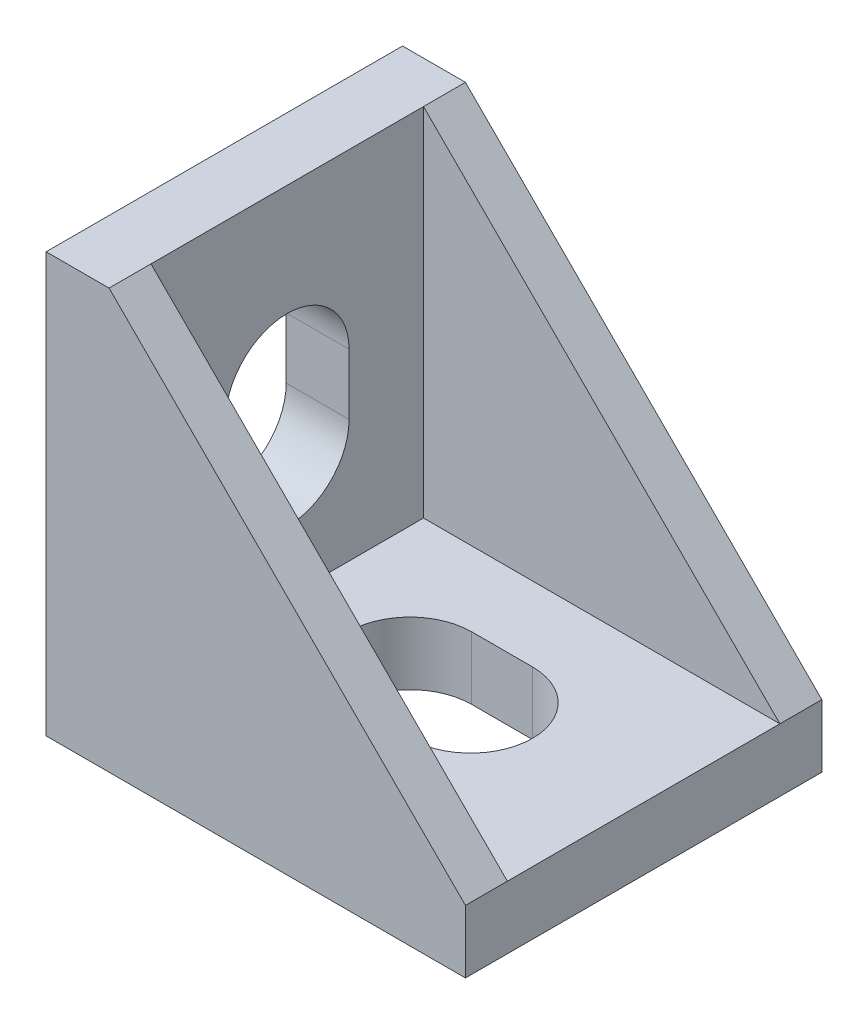
SolidWorks part; units mm, degrees
ref_plane "前视基准面" through (0, 0, 0) normal (0, 0, 1) x (1, 0, 0)
ref_plane "上视基准面" through (0, 0, 0) normal (0, 1, 0) x (1, 0, 0)
ref_plane "右视基准面" through (0, 0, 0) normal (1, 0, 0) x (0, 0, -1)
sketch "草图1" plane through (0, 0, 0) normal (0, 0, 1) x (1, 0, 0)
  line L0 (0, 0) -> (20, 0)
  line L1 (20, 0) -> (20, 3)
  line L2 (0, 0) -> (0, 20)
  line L3 (0, 20) -> (3, 20)
  line L4 (3, 20) -> (20, 3)
  dimension "D1" = 20
  dimension "D2" = 20
  dimension "D3" = 3
  dimension "D4" = 3
extrude "凸台-拉伸1" add sketch "草图1" along normal blind 17
ref_plane "基准面1" through (0, 3, 0) normal (0, -1, 0) x (-1, 0, 0)
sketch "草图2" plane through (0, 3, 0) normal (0, -1, 0) x (-1, 0, 0)
  line L0 (-20, 0) -> (-20, -2)
  line L1 (-20, -17) -> (-20, 0) construction
  line L3 (-20, -2) -> (-3, -2)
  line L4 (-20, -2) -> (-20, -15)
  line L5 (-20, -15) -> (-3, -15)
  line L6 (-3, -2) -> (-3, -15)
  dimension "D1" = 2
  dimension "D2" = 17
  dimension "D3" = 13
extrude "切除-拉伸1" cut sketch "草图2" against normal through all contours L3 L6 L5 L4
sketch "草图5" plane through (0, 3, 0) normal (0, 1, 0) x (1, 0, 0)
  line L0 (20, -8.5) -> (11.75, -8.5)
  line L1 (20, -2) -> (20, -15) construction
  line L2 (11.75, -8.5) -> (8.85, -8.5) construction
  line L3 (11.75, -11.45) -> (8.85, -11.45)
  line L4 (11.75, -5.55) -> (8.85, -5.55)
  arc A0 (11.75, -11.45) -> (11.75, -5.55) centre (11.75, -8.5) ccw
  arc A1 (8.85, -5.55) -> (8.85, -11.45) centre (8.85, -8.5) ccw
  point P4 (10.3, -8.5)
  dimension "D3" = 2.95
  dimension "D1" = 8.25
  dimension "D2" = 2.9
extrude "切除-拉伸2" cut sketch "草图5" against normal through all
ref_plane "基准面2" through (0, 0, 0) normal (0.7071, -0.7071, 0) x (0, 0, -1)
mirror "镜向1" about plane through (0, 0, 0) normal (0.7071, -0.7071, 0) of "切除-拉伸2"
